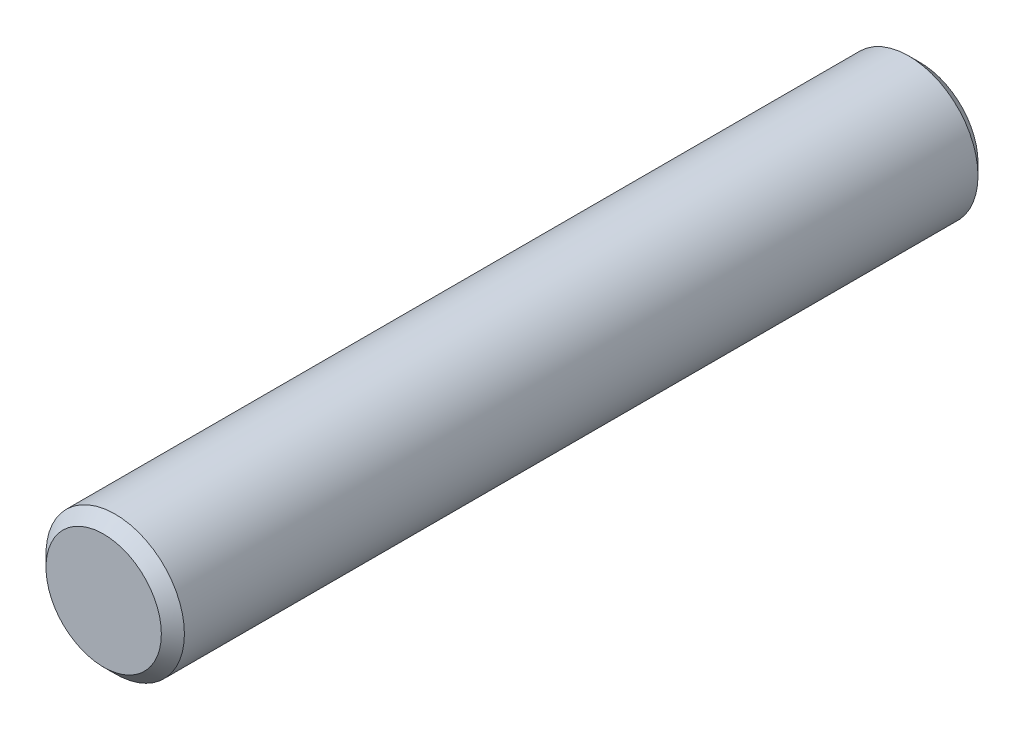
SolidWorks part; units mm, degrees
material "Plain Carbon Steel"
ref_plane "Front Plane" through (0, 0, 0) normal (0, 0, 1) x (1, 0, 0)
ref_plane "Top Plane" through (0, 0, 0) normal (0, 1, 0) x (1, 0, 0)
ref_plane "Right Plane" through (0, 0, 0) normal (1, 0, 0) x (0, 0, -1)
sketch "Sketch1" plane through (0, 0, 0) normal (0, 0, 1) x (1, 0, 0)
  circle A0 centre (0, 0) radius 4.7625
  dimension "D1" = 9.525
extrude "Boss-Extrude1" add sketch "Sketch1" along normal blind 56.2
chamfer "Chamfer1" distance 0.7937 angle 45 2 edges at (4.7625, 0, 0) (4.7625, 0, 56.2)
